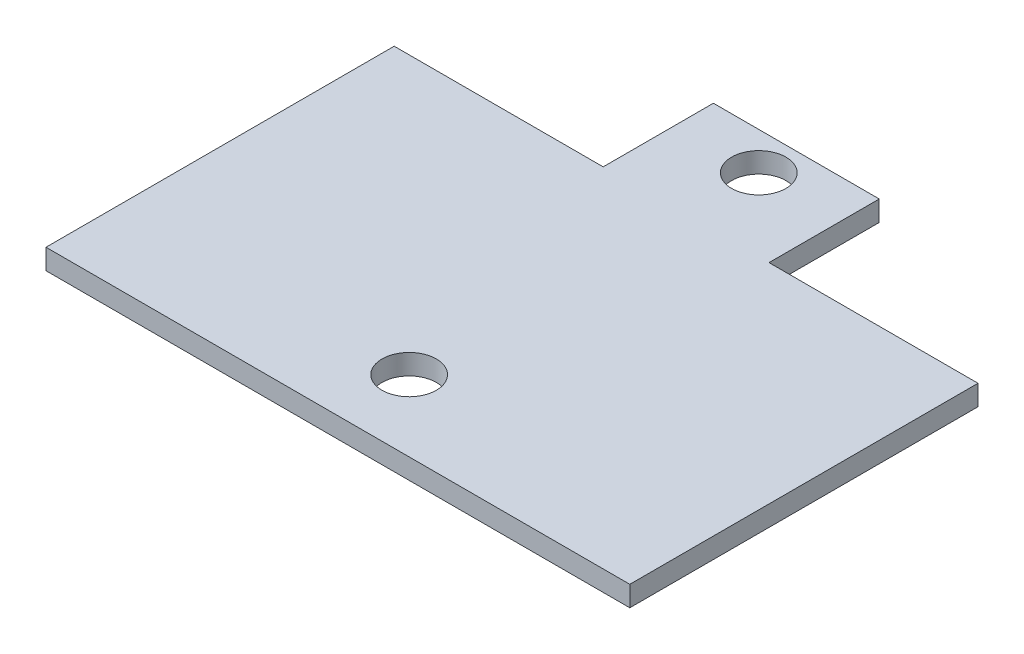
SolidWorks part; units mm, degrees
ref_plane "Спереди" through (0, 0, 0) normal (0, 0, 1) x (1, 0, 0)
ref_plane "Сверху" through (0, 0, 0) normal (0, 1, 0) x (1, 0, 0)
ref_plane "Справа" through (0, 0, 0) normal (1, 0, 0) x (0, 0, -1)
sketch "Эскиз1" plane through (0, 0, 0) normal (0, 1, 0) x (1, 0, 0)
  line L0 (0, 25.6465) -> (15.3923, 25.6465)
  line L1 (0, 0) -> (43, 0)
  line L2 (0, 0) -> (0, 25.6465)
  line L4 (43, 0) -> (43, 25.6465)
  line L5 (15.3923, 25.6465) -> (15.3923, 33.7649)
  line L6 (15.3923, 33.7649) -> (27.6077, 33.7649)
  line L7 (27.6077, 33.7649) -> (27.6077, 25.6465)
  line L8 (27.6077, 25.6465) -> (43, 25.6465)
  line L9 (21.5, 0) -> (21.5, 67.5298) construction
  circle A1 centre (21.5, 5.25) radius 2
  circle A2 centre (21.5, 31) radius 2
  point P13 (21.5, 33.7649)
  point P14 (21.5, 31.5311)
  point P15 (21.5, 5.7915)
  point P16 (21.6056, 6.2227)
  point P19 (0, 0)
extrude "Бобышка-Вытянуть1" add sketch "Эскиз1" along normal blind 1.5
